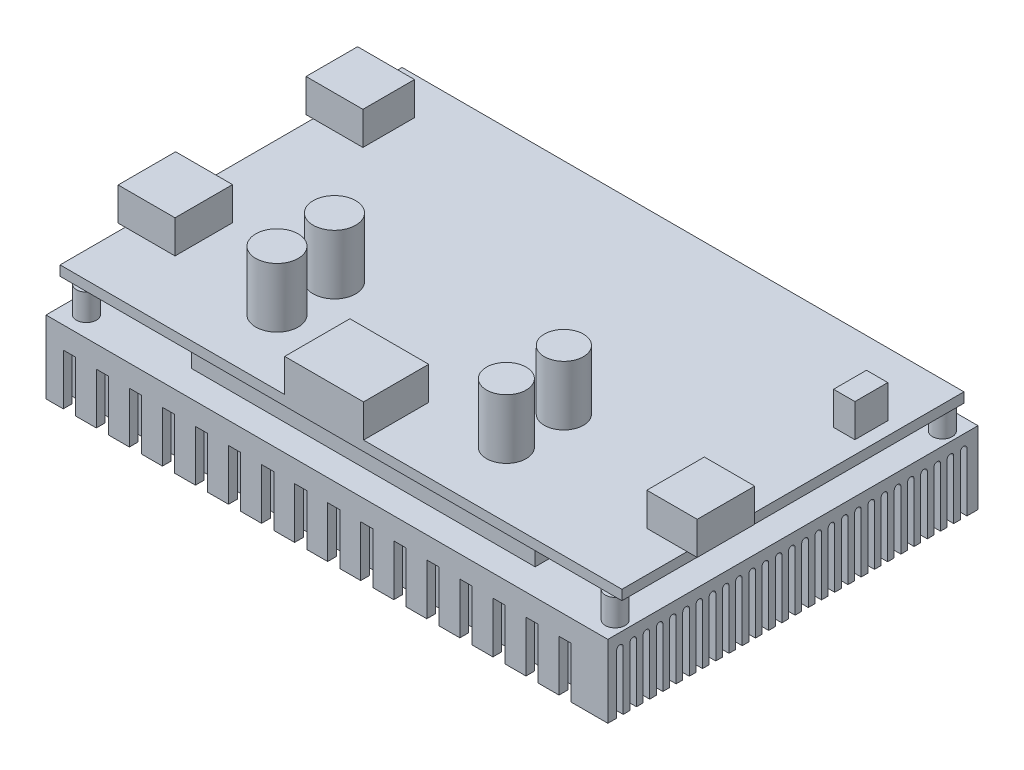
SolidWorks part; units mm, degrees
ref_plane "前视基准面" through (0, 0, 0) normal (0, 0, 1) x (1, 0, 0)
ref_plane "上视基准面" through (0, 0, 0) normal (0, 1, 0) x (1, 0, 0)
ref_plane "右视基准面" through (0, 0, 0) normal (1, 0, 0) x (0, 0, -1)
sketch "草图1" plane through (0, 0, 0) normal (0, 1, 0) x (1, 0, 0)
  line L1 (-42.5, -28) -> (42.5, -28)
  line L2 (-42.5, -28) -> (-42.5, 28)
  line L3 (-42.5, 28) -> (42.5, 28)
  line L4 (42.5, -28) -> (42.5, 28)
  line L5 (-42.5, -28) -> (42.5, 28) construction
  line L6 (-42.5, 28) -> (42.5, -28) construction
  point P0 (0, 0)
  dimension "D1" = 56
  dimension "D2" = 85
extrude "凸台-拉伸1" add sketch "草图1" along normal blind 11
sketch "草图2" plane through (0, 11, 0) normal (0, 1, 0) x (1, 0, 0)
  line L0 (-42.5, -28) -> (42.5, -28) construction
  line L1 (-24.5, -24) -> (27.5, -24)
  line L2 (-24.5, -24) -> (-24.5, 11)
  line L3 (-24.5, 11) -> (27.5, 11)
  line L4 (27.5, -24) -> (27.5, 11)
  line L5 (-42.5, 28) -> (-42.5, -28) construction
  circle A0 centre (-39.5, 24.6153) radius 1.5
  circle A1 centre (40.5, 24.6153) radius 1.5
  circle A2 centre (40.5, -24.8843) radius 1.5
  circle A3 centre (-39.5, -24.8843) radius 1.5
  point P0 (0, 0)
  dimension "D1" = 3
  dimension "D2" = 3
  dimension "D3" = 3
  dimension "D4" = 3
  dimension "D5" = 4
  dimension "D6" = 35
  dimension "D7" = 52
  dimension "D8" = 18
  dimension "D9" = 80
  dimension "D10" = 3
  dimension "D11" = 80
  dimension "D12" = 3
extrude "凸台-拉伸2" add sketch "草图2" along normal blind 4
sketch "草图3" plane through (0, 15, 0) normal (0, 1, 0) x (1, 0, 0)
  line L0 (42.5, -28) -> (42.5, 28) construction
  line L1 (-42.5, -25.8708) -> (42.5, -25.8708)
  line L2 (-42.5, -25.8708) -> (-42.5, 25.8708)
  line L3 (-42.5, 25.8708) -> (42.5, 25.8708)
  line L4 (42.5, -25.8708) -> (42.5, 25.8708)
  line L5 (-42.5, -25.8708) -> (42.5, 25.8708) construction
  line L6 (-42.5, 25.8708) -> (42.5, -25.8708) construction
  point P0 (0, 0)
extrude "凸台-拉伸3" add sketch "草图3" along normal blind 1.5
sketch "草图4" plane through (0, 16.5, 0) normal (0, 1, 0) x (1, 0, 0)
  line L0 (-42.5, -25.8708) -> (42.5, -25.8708) construction
  line L1 (-43.5812, 20.2213) -> (-34.9726, 20.2213)
  line L2 (-43.5812, 20.2213) -> (-43.5812, 12.4198)
  line L3 (-43.5812, 12.4198) -> (-34.9726, 12.4198)
  line L4 (-34.9726, 20.2213) -> (-34.9726, 12.4198)
  line L5 (-43.5812, -7.3084) -> (-34.9726, -7.3084)
  line L6 (-43.5812, -7.3084) -> (-43.5812, -16.0067)
  line L7 (-43.5812, -16.0067) -> (-34.9726, -16.0067)
  line L8 (-34.9726, -7.3084) -> (-34.9726, -16.0067)
  line L9 (37.3041, 16.3205) -> (40.5323, 16.3205)
  line L10 (37.3041, 16.3205) -> (37.3041, 11.3437)
  line L11 (37.3041, 11.3437) -> (40.5323, 11.3437)
  line L12 (40.5323, 16.3205) -> (40.5323, 11.3437)
  line L13 (36.4074, -7.3084) -> (44.0296, -7.3084)
  line L14 (36.4074, -7.3084) -> (36.4074, -16.0067)
  line L15 (36.4074, -16.0067) -> (44.0296, -16.0067)
  line L16 (44.0296, -7.3084) -> (44.0296, -16.0067)
  line L17 (-8.519, -25.8708) -> (3.4076, -25.8708)
  line L18 (-8.519, -25.8708) -> (-8.519, -16.0067)
  line L19 (-8.519, -16.0067) -> (3.4076, -16.0067)
  line L20 (3.4076, -25.8708) -> (3.4076, -16.0067)
  circle A0 centre (-19.5488, -7.3084) radius 3.2195
  circle A1 centre (-19.5488, -16.0067) radius 3.2145
  circle A2 centre (15.1548, -7.3084) radius 2.9592
  circle A3 centre (15.1548, -16.0067) radius 3
  dimension "D1" = 6
extrude "凸台-拉伸4" add sketch "草图4" along normal blind 5
sketch "草图5" plane through (0, 21.5, 0) normal (0, 1, 0) x (1, 0, 0)
  circle A0 centre (15.1548, -16.0067) radius 3 construction
  circle A1 centre (15.1548, -7.3084) radius 2.9592 construction
  circle A2 centre (-19.5488, -16.0067) radius 3.2145 construction
  circle A3 centre (-19.5488, -7.3084) radius 3.2195 construction
  circle A4 centre (15.1548, -16.0067) radius 3
  circle A5 centre (15.1548, -7.3084) radius 2.9592
  circle A6 centre (-19.5488, -16.0067) radius 3.2145
  circle A7 centre (-19.5488, -7.3084) radius 3.2195
extrude "凸台-拉伸5" add sketch "草图5" along normal blind 4
sketch "草图6" plane through (-43.5812, 0, 0) normal (-1, 0, 0) x (0, 0, 1)
  line L1 (-13.7654, 17.2695) -> (-18.728, 17.2695)
  line L2 (-13.7654, 17.2695) -> (-13.7654, 20.3416)
  line L3 (-13.7654, 20.3416) -> (-18.728, 20.3416)
  line L4 (-18.728, 17.2695) -> (-18.728, 20.3416)
  line L5 (8.5664, 17.2695) -> (14.238, 17.2695)
  line L6 (8.5664, 17.2695) -> (8.5664, 20.3416)
  line L7 (8.5664, 20.3416) -> (14.238, 20.3416)
  line L8 (14.238, 17.2695) -> (14.238, 20.3416)
extrude "切除-拉伸1" cut sketch "草图6" against normal blind 4
sketch "草图7" plane through (42.5, 0, 0) normal (1, 0, 0) x (0, 0, -1)
  line L0 (-26.1719, 8.8803) -> (-26.1719, -2.581) construction
  line L1 (-25.6719, 8.8803) -> (-25.6719, -2.581)
  line L2 (-26.6719, 8.8803) -> (-26.6719, -2.581)
  line L3 (-24.1719, 8.8803) -> (-24.1719, -2.581) construction
  line L4 (-23.6719, 8.8803) -> (-23.6719, -2.581)
  line L5 (-24.6719, 8.8803) -> (-24.6719, -2.581)
  line L6 (-22.1719, 8.8803) -> (-22.1719, -2.581) construction
  line L7 (-21.6719, 8.8803) -> (-21.6719, -2.581)
  line L8 (-22.6719, 8.8803) -> (-22.6719, -2.581)
  line L9 (-20.1719, 8.8803) -> (-20.1719, -2.581) construction
  line L10 (-19.6719, 8.8803) -> (-19.6719, -2.581)
  line L11 (-20.6719, 8.8803) -> (-20.6719, -2.581)
  line L12 (-18.1719, 8.8803) -> (-18.1719, -2.581) construction
  line L13 (-17.6719, 8.8803) -> (-17.6719, -2.581)
  line L14 (-18.6719, 8.8803) -> (-18.6719, -2.581)
  line L15 (-16.1719, 8.8803) -> (-16.1719, -2.581) construction
  line L16 (-15.6719, 8.8803) -> (-15.6719, -2.581)
  line L17 (-16.6719, 8.8803) -> (-16.6719, -2.581)
  line L18 (-14.1719, 8.8803) -> (-14.1719, -2.581) construction
  line L19 (-13.6719, 8.8803) -> (-13.6719, -2.581)
  line L20 (-14.6719, 8.8803) -> (-14.6719, -2.581)
  line L21 (-12.1719, 8.8803) -> (-12.1719, -2.581) construction
  line L22 (-11.6719, 8.8803) -> (-11.6719, -2.581)
  line L23 (-12.6719, 8.8803) -> (-12.6719, -2.581)
  line L24 (-10.1719, 8.8803) -> (-10.1719, -2.581) construction
  line L25 (-9.6719, 8.8803) -> (-9.6719, -2.581)
  line L26 (-10.6719, 8.8803) -> (-10.6719, -2.581)
  line L27 (-8.1719, 8.8803) -> (-8.1719, -2.581) construction
  line L28 (-7.6719, 8.8803) -> (-7.6719, -2.581)
  line L29 (-8.6719, 8.8803) -> (-8.6719, -2.581)
  line L30 (-6.1719, 8.8803) -> (-6.1719, -2.581) construction
  line L31 (-5.6719, 8.8803) -> (-5.6719, -2.581)
  line L32 (-6.6719, 8.8803) -> (-6.6719, -2.581)
  line L33 (-4.1719, 8.8803) -> (-4.1719, -2.581) construction
  line L34 (-3.6719, 8.8803) -> (-3.6719, -2.581)
  line L35 (-4.6719, 8.8803) -> (-4.6719, -2.581)
  line L36 (-2.1719, 8.8803) -> (-2.1719, -2.581) construction
  line L37 (-1.6719, 8.8803) -> (-1.6719, -2.581)
  line L38 (-2.6719, 8.8803) -> (-2.6719, -2.581)
  line L39 (-0.1719, 8.8803) -> (-0.1719, -2.581) construction
  line L40 (0.3281, 8.8803) -> (0.3281, -2.581)
  line L41 (-0.6719, 8.8803) -> (-0.6719, -2.581)
  line L42 (1.8281, 8.8803) -> (1.8281, -2.581) construction
  line L43 (2.3281, 8.8803) -> (2.3281, -2.581)
  line L44 (1.3281, 8.8803) -> (1.3281, -2.581)
  line L45 (3.8281, 8.8803) -> (3.8281, -2.581) construction
  line L46 (4.3281, 8.8803) -> (4.3281, -2.581)
  line L47 (3.3281, 8.8803) -> (3.3281, -2.581)
  line L48 (5.8281, 8.8803) -> (5.8281, -2.581) construction
  line L49 (6.3281, 8.8803) -> (6.3281, -2.581)
  line L50 (5.3281, 8.8803) -> (5.3281, -2.581)
  line L51 (7.8281, 8.8803) -> (7.8281, -2.581) construction
  line L52 (8.3281, 8.8803) -> (8.3281, -2.581)
  line L53 (7.3281, 8.8803) -> (7.3281, -2.581)
  line L54 (9.8281, 8.8803) -> (9.8281, -2.581) construction
  line L55 (10.3281, 8.8803) -> (10.3281, -2.581)
  line L56 (9.3281, 8.8803) -> (9.3281, -2.581)
  line L57 (11.8281, 8.8803) -> (11.8281, -2.581) construction
  line L58 (12.3281, 8.8803) -> (12.3281, -2.581)
  line L59 (11.3281, 8.8803) -> (11.3281, -2.581)
  line L60 (13.8281, 8.8803) -> (13.8281, -2.581) construction
  line L61 (14.3281, 8.8803) -> (14.3281, -2.581)
  line L62 (13.3281, 8.8803) -> (13.3281, -2.581)
  line L63 (15.8281, 8.8803) -> (15.8281, -2.581) construction
  line L64 (16.3281, 8.8803) -> (16.3281, -2.581)
  line L65 (15.3281, 8.8803) -> (15.3281, -2.581)
  line L66 (17.8281, 8.8803) -> (17.8281, -2.581) construction
  line L67 (18.3281, 8.8803) -> (18.3281, -2.581)
  line L68 (17.3281, 8.8803) -> (17.3281, -2.581)
  line L69 (19.8281, 8.8803) -> (19.8281, -2.581) construction
  line L70 (20.3281, 8.8803) -> (20.3281, -2.581)
  line L71 (19.3281, 8.8803) -> (19.3281, -2.581)
  line L72 (21.8281, 8.8803) -> (21.8281, -2.581) construction
  line L73 (22.3281, 8.8803) -> (22.3281, -2.581)
  line L74 (21.3281, 8.8803) -> (21.3281, -2.581)
  line L75 (23.8281, 8.8803) -> (23.8281, -2.581) construction
  line L76 (24.3281, 8.8803) -> (24.3281, -2.581)
  line L77 (23.3281, 8.8803) -> (23.3281, -2.581)
  line L78 (25.8281, 8.8803) -> (25.8281, -2.581) construction
  line L79 (26.3281, 8.8803) -> (26.3281, -2.581)
  line L80 (25.3281, 8.8803) -> (25.3281, -2.581)
  arc A0 (-25.6719, 8.8803) -> (-26.6719, 8.8803) centre (-26.1719, 8.8803) ccw
  arc A1 (-26.6719, -2.581) -> (-25.6719, -2.581) centre (-26.1719, -2.581) ccw
  arc A2 (-23.6719, 8.8803) -> (-24.6719, 8.8803) centre (-24.1719, 8.8803) ccw
  arc A3 (-24.6719, -2.581) -> (-23.6719, -2.581) centre (-24.1719, -2.581) ccw
  arc A4 (-21.6719, 8.8803) -> (-22.6719, 8.8803) centre (-22.1719, 8.8803) ccw
  arc A5 (-22.6719, -2.581) -> (-21.6719, -2.581) centre (-22.1719, -2.581) ccw
  arc A6 (-19.6719, 8.8803) -> (-20.6719, 8.8803) centre (-20.1719, 8.8803) ccw
  arc A7 (-20.6719, -2.581) -> (-19.6719, -2.581) centre (-20.1719, -2.581) ccw
  arc A8 (-17.6719, 8.8803) -> (-18.6719, 8.8803) centre (-18.1719, 8.8803) ccw
  arc A9 (-18.6719, -2.581) -> (-17.6719, -2.581) centre (-18.1719, -2.581) ccw
  arc A10 (-15.6719, 8.8803) -> (-16.6719, 8.8803) centre (-16.1719, 8.8803) ccw
  arc A11 (-16.6719, -2.581) -> (-15.6719, -2.581) centre (-16.1719, -2.581) ccw
  arc A12 (-13.6719, 8.8803) -> (-14.6719, 8.8803) centre (-14.1719, 8.8803) ccw
  arc A13 (-14.6719, -2.581) -> (-13.6719, -2.581) centre (-14.1719, -2.581) ccw
  arc A14 (-11.6719, 8.8803) -> (-12.6719, 8.8803) centre (-12.1719, 8.8803) ccw
  arc A15 (-12.6719, -2.581) -> (-11.6719, -2.581) centre (-12.1719, -2.581) ccw
  arc A16 (-9.6719, 8.8803) -> (-10.6719, 8.8803) centre (-10.1719, 8.8803) ccw
  arc A17 (-10.6719, -2.581) -> (-9.6719, -2.581) centre (-10.1719, -2.581) ccw
  arc A18 (-7.6719, 8.8803) -> (-8.6719, 8.8803) centre (-8.1719, 8.8803) ccw
  arc A19 (-8.6719, -2.581) -> (-7.6719, -2.581) centre (-8.1719, -2.581) ccw
  arc A20 (-5.6719, 8.8803) -> (-6.6719, 8.8803) centre (-6.1719, 8.8803) ccw
  arc A21 (-6.6719, -2.581) -> (-5.6719, -2.581) centre (-6.1719, -2.581) ccw
  arc A22 (-3.6719, 8.8803) -> (-4.6719, 8.8803) centre (-4.1719, 8.8803) ccw
  arc A23 (-4.6719, -2.581) -> (-3.6719, -2.581) centre (-4.1719, -2.581) ccw
  arc A24 (-1.6719, 8.8803) -> (-2.6719, 8.8803) centre (-2.1719, 8.8803) ccw
  arc A25 (-2.6719, -2.581) -> (-1.6719, -2.581) centre (-2.1719, -2.581) ccw
  arc A26 (0.3281, 8.8803) -> (-0.6719, 8.8803) centre (-0.1719, 8.8803) ccw
  arc A27 (-0.6719, -2.581) -> (0.3281, -2.581) centre (-0.1719, -2.581) ccw
  arc A28 (2.3281, 8.8803) -> (1.3281, 8.8803) centre (1.8281, 8.8803) ccw
  arc A29 (1.3281, -2.581) -> (2.3281, -2.581) centre (1.8281, -2.581) ccw
  arc A30 (4.3281, 8.8803) -> (3.3281, 8.8803) centre (3.8281, 8.8803) ccw
  arc A31 (3.3281, -2.581) -> (4.3281, -2.581) centre (3.8281, -2.581) ccw
  arc A32 (6.3281, 8.8803) -> (5.3281, 8.8803) centre (5.8281, 8.8803) ccw
  arc A33 (5.3281, -2.581) -> (6.3281, -2.581) centre (5.8281, -2.581) ccw
  arc A34 (8.3281, 8.8803) -> (7.3281, 8.8803) centre (7.8281, 8.8803) ccw
  arc A35 (7.3281, -2.581) -> (8.3281, -2.581) centre (7.8281, -2.581) ccw
  arc A36 (10.3281, 8.8803) -> (9.3281, 8.8803) centre (9.8281, 8.8803) ccw
  arc A37 (9.3281, -2.581) -> (10.3281, -2.581) centre (9.8281, -2.581) ccw
  arc A38 (12.3281, 8.8803) -> (11.3281, 8.8803) centre (11.8281, 8.8803) ccw
  arc A39 (11.3281, -2.581) -> (12.3281, -2.581) centre (11.8281, -2.581) ccw
  arc A40 (14.3281, 8.8803) -> (13.3281, 8.8803) centre (13.8281, 8.8803) ccw
  arc A41 (13.3281, -2.581) -> (14.3281, -2.581) centre (13.8281, -2.581) ccw
  arc A42 (16.3281, 8.8803) -> (15.3281, 8.8803) centre (15.8281, 8.8803) ccw
  arc A43 (15.3281, -2.581) -> (16.3281, -2.581) centre (15.8281, -2.581) ccw
  arc A44 (18.3281, 8.8803) -> (17.3281, 8.8803) centre (17.8281, 8.8803) ccw
  arc A45 (17.3281, -2.581) -> (18.3281, -2.581) centre (17.8281, -2.581) ccw
  arc A46 (20.3281, 8.8803) -> (19.3281, 8.8803) centre (19.8281, 8.8803) ccw
  arc A47 (19.3281, -2.581) -> (20.3281, -2.581) centre (19.8281, -2.581) ccw
  arc A48 (22.3281, 8.8803) -> (21.3281, 8.8803) centre (21.8281, 8.8803) ccw
  arc A49 (21.3281, -2.581) -> (22.3281, -2.581) centre (21.8281, -2.581) ccw
  arc A50 (24.3281, 8.8803) -> (23.3281, 8.8803) centre (23.8281, 8.8803) ccw
  arc A51 (23.3281, -2.581) -> (24.3281, -2.581) centre (23.8281, -2.581) ccw
  arc A52 (26.3281, 8.8803) -> (25.3281, 8.8803) centre (25.8281, 8.8803) ccw
  arc A53 (25.3281, -2.581) -> (26.3281, -2.581) centre (25.8281, -2.581) ccw
  point P2 (-26.1719, 3.1497)
  point P11 (-24.1719, 3.1497)
  point P18 (-22.1719, 3.1497)
  point P25 (-20.1719, 3.1497)
  point P32 (-18.1719, 3.1497)
  point P39 (-16.1719, 3.1497)
  point P46 (-14.1719, 3.1497)
  point P53 (-12.1719, 3.1497)
  point P60 (-10.1719, 3.1497)
  point P67 (-8.1719, 3.1497)
  point P74 (-6.1719, 3.1497)
  point P81 (-4.1719, 3.1497)
  point P88 (-2.1719, 3.1497)
  point P95 (-0.1719, 3.1497)
  point P102 (1.8281, 3.1497)
  point P109 (3.8281, 3.1497)
  point P116 (5.8281, 3.1497)
  point P123 (7.8281, 3.1497)
  point P130 (9.8281, 3.1497)
  point P137 (11.8281, 3.1497)
  point P144 (13.8281, 3.1497)
  point P151 (15.8281, 3.1497)
  point P158 (17.8281, 3.1497)
  point P165 (19.8281, 3.1497)
  point P172 (21.8281, 3.1497)
  point P179 (23.8281, 3.1497)
  point P186 (25.8281, 3.1497)
  dimension "D1" = 27
extrude "切除-拉伸2" cut sketch "草图7" against normal through all
sketch "草图8" plane through (0, 0, 28) normal (0, 0, 1) x (1, 0, 0)
  line L0 (-42.5, 0) -> (42.5, 0) construction
  line L1 (-39.8894, 0) -> (-38.0409, 0)
  line L2 (-39.8894, 0) -> (-39.8894, 7.7127)
  line L3 (-39.8894, 7.7127) -> (-38.0409, 7.7127)
  line L4 (-38.0409, 0) -> (-38.0409, 7.7127)
  line L5 (-34.8894, 0) -> (-34.8894, 7.7127)
  line L6 (-34.8894, 0) -> (-33.0409, 0)
  line L7 (-33.0409, 0) -> (-33.0409, 7.7127)
  line L8 (-34.8894, 7.7127) -> (-33.0409, 7.7127)
  line L9 (-29.8894, 0) -> (-29.8894, 7.7127)
  line L10 (-29.8894, 0) -> (-28.0409, 0)
  line L11 (-28.0409, 0) -> (-28.0409, 7.7127)
  line L12 (-29.8894, 7.7127) -> (-28.0409, 7.7127)
  line L13 (-24.8894, 0) -> (-24.8894, 7.7127)
  line L14 (-24.8894, 0) -> (-23.0409, 0)
  line L15 (-23.0409, 0) -> (-23.0409, 7.7127)
  line L16 (-24.8894, 7.7127) -> (-23.0409, 7.7127)
  line L17 (-19.8894, 0) -> (-19.8894, 7.7127)
  line L18 (-19.8894, 0) -> (-18.0409, 0)
  line L19 (-18.0409, 0) -> (-18.0409, 7.7127)
  line L20 (-19.8894, 7.7127) -> (-18.0409, 7.7127)
  line L21 (-14.8894, 0) -> (-14.8894, 7.7127)
  line L22 (-14.8894, 0) -> (-13.0409, 0)
  line L23 (-13.0409, 0) -> (-13.0409, 7.7127)
  line L24 (-14.8894, 7.7127) -> (-13.0409, 7.7127)
  line L25 (-9.8894, 0) -> (-9.8894, 7.7127)
  line L26 (-9.8894, 0) -> (-8.0409, 0)
  line L27 (-8.0409, 0) -> (-8.0409, 7.7127)
  line L28 (-9.8894, 7.7127) -> (-8.0409, 7.7127)
  line L29 (-4.8894, 0) -> (-4.8894, 7.7127)
  line L30 (-4.8894, 0) -> (-3.0409, 0)
  line L31 (-3.0409, 0) -> (-3.0409, 7.7127)
  line L32 (-4.8894, 7.7127) -> (-3.0409, 7.7127)
  line L33 (0.1106, 0) -> (0.1106, 7.7127)
  line L34 (0.1106, 0) -> (1.9591, 0)
  line L35 (1.9591, 0) -> (1.9591, 7.7127)
  line L36 (0.1106, 7.7127) -> (1.9591, 7.7127)
  line L37 (5.1106, 0) -> (5.1106, 7.7127)
  line L38 (5.1106, 0) -> (6.9591, 0)
  line L39 (6.9591, 0) -> (6.9591, 7.7127)
  line L40 (5.1106, 7.7127) -> (6.9591, 7.7127)
  line L41 (10.1106, 0) -> (10.1106, 7.7127)
  line L42 (10.1106, 0) -> (11.9591, 0)
  line L43 (11.9591, 0) -> (11.9591, 7.7127)
  line L44 (10.1106, 7.7127) -> (11.9591, 7.7127)
  line L45 (15.1106, 0) -> (15.1106, 7.7127)
  line L46 (15.1106, 0) -> (16.9591, 0)
  line L47 (16.9591, 0) -> (16.9591, 7.7127)
  line L48 (15.1106, 7.7127) -> (16.9591, 7.7127)
  line L49 (20.1106, 0) -> (20.1106, 7.7127)
  line L50 (20.1106, 0) -> (21.9591, 0)
  line L51 (21.9591, 0) -> (21.9591, 7.7127)
  line L52 (20.1106, 7.7127) -> (21.9591, 7.7127)
  line L53 (25.1106, 0) -> (25.1106, 7.7127)
  line L54 (25.1106, 0) -> (26.9591, 0)
  line L55 (26.9591, 0) -> (26.9591, 7.7127)
  line L56 (25.1106, 7.7127) -> (26.9591, 7.7127)
  line L57 (30.1106, 0) -> (30.1106, 7.7127)
  line L58 (30.1106, 0) -> (31.9591, 0)
  line L59 (31.9591, 0) -> (31.9591, 7.7127)
  line L60 (30.1106, 7.7127) -> (31.9591, 7.7127)
  line L61 (35.1106, 0) -> (35.1106, 7.7127)
  line L62 (35.1106, 0) -> (36.9591, 0)
  line L63 (36.9591, 0) -> (36.9591, 7.7127)
  line L64 (35.1106, 7.7127) -> (36.9591, 7.7127)
  dimension "D1" = 16
extrude "切除-拉伸3" cut sketch "草图8" against normal through all
